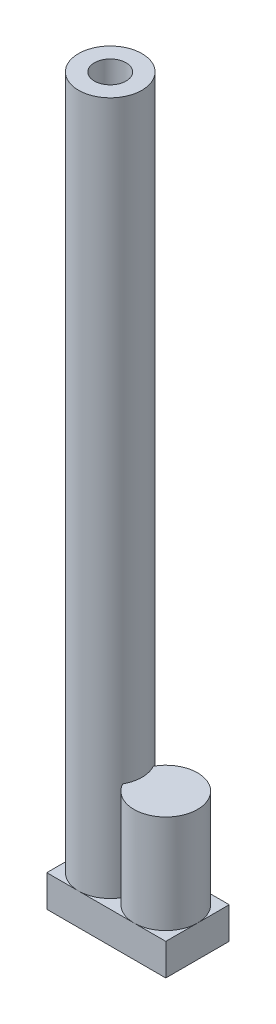
SolidWorks part; units mm, degrees
ref_plane "Front Plane" through (0, 0, 0) normal (0, 0, 1) x (1, 0, 0)
ref_plane "Top Plane" through (0, 0, 0) normal (0, 1, 0) x (1, 0, 0)
ref_plane "Right Plane" through (0, 0, 0) normal (1, 0, 0) x (0, 0, -1)
sketch "Sketch1" plane through (0, 0, 0) normal (0, 1, 0) x (1, 0, 0)
  circle A0 centre (0, 0) radius 20
  dimension "D1" = 40
extrude "Boss-Extrude1" add sketch "Sketch1" along normal blind 457
sketch "Sketch2" plane through (0, 457, 0) normal (0, 1, 0) x (1, 0, 0)
  circle A0 centre (0, 0) radius 10
  dimension "D1" = 20
extrude "Cut-Extrude1" cut sketch "Sketch2" against normal blind 526
sketch "Sketch6" plane through (0, 0, 0) normal (0, -1, 0) x (1, 0, 0)
  circle A0 centre (35, 0) radius 20
  dimension "D1" = 40
  dimension "D2" = 35
extrude "Boss-Extrude4" add sketch "Sketch6" against normal blind 82
sketch "Sketch7" plane through (0, 0, 0) normal (0, -1, 0) x (1, 0, 0)
  line L1 (-20, 20) -> (55, 20)
  line L2 (-20, 20) -> (-20, -20)
  line L3 (-20, -20) -> (55, -20)
  line L4 (55, 20) -> (55, -20)
  arc A0 (17.5, -9.6825) -> (17.5, 9.6825) centre (35, 0) ccw construction
  arc A1 (17.5, 9.6825) -> (17.5, -9.6825) centre (0, 0) ccw construction
extrude "Boss-Extrude5" add sketch "Sketch7" against normal blind 20
